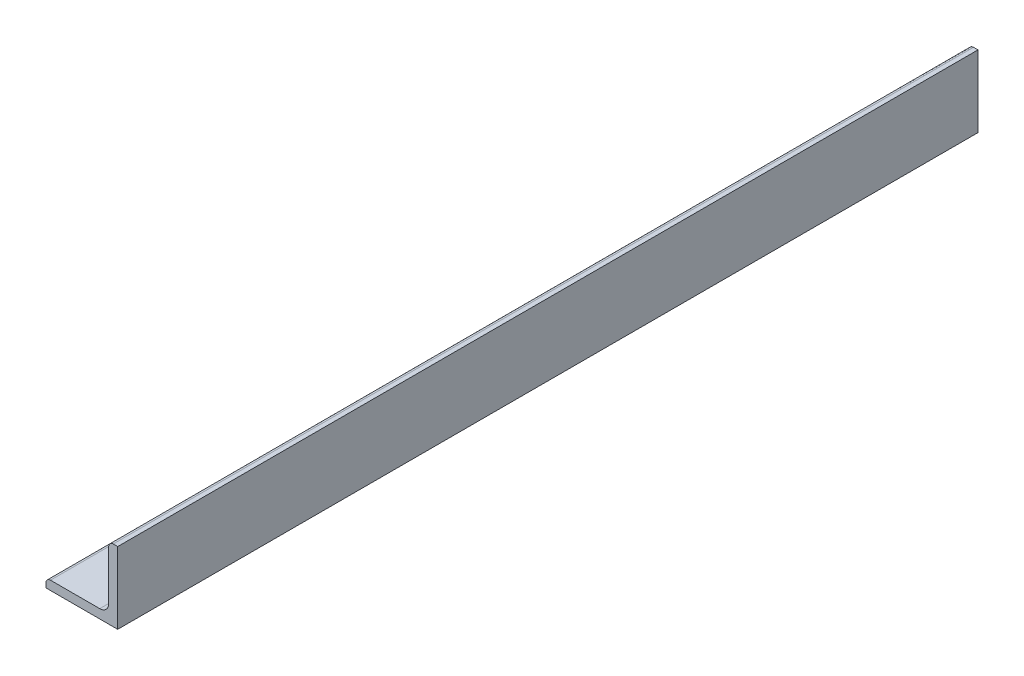
SolidWorks part; units mm, degrees
ref_plane "Front Plane" through (0, 0, 0) normal (0, 0, 1) x (1, 0, 0)
ref_plane "Top Plane" through (0, 0, 0) normal (0, 1, 0) x (1, 0, 0)
ref_plane "Right Plane" through (0, 0, 0) normal (1, 0, 0) x (0, 0, -1)
sketch "Sketch0" plane through (0, 0, 0) normal (0, 0, 1) x (1, 0, 0)
  line L0 (-12.7, -12.7) -> (12.7, -12.7)
  line L1 (12.7, -12.7) -> (12.7, 12.7)
  line L2 (12.7, 0) -> (0, 0) construction
  line L3 (0, 0) -> (0, -12.7) construction
  line L4 (9.525, -6.35) -> (9.525, 12.7) construction
  line L5 (6.35, -9.525) -> (-12.7, -9.525) construction
  arc A0 (9.525, -6.35) -> (6.35, -9.525) centre (6.35, -6.35) cw
  point P3 (8.5951, -8.5951)
  dimension "Inside Corner Radius" = 3.175
  dimension "Outside Height" = 25.4
  dimension "Inside Height" = 22.225
  dimension "Inside Width" = 22.225
  dimension "Wall Thickness" = 3.175
  dimension "D1" = 3.175
  dimension "Outside Width" = 25.4
sketch "Sketch1" plane through (0, 0, 0) normal (1, 0, 0) x (0, 0, -1)
  line L0 (152.4, 0) -> (-152.4, 0)
  point P4 (0, 0)
  dimension "Length" = 304.8
sketch "Sketch2" plane through (0, 0, 0) normal (0, 0, 1) x (1, 0, 0)
  line L0 (-12.7, -12.7) -> (12.7, -12.7)
  line L1 (12.7, -12.7) -> (12.7, 12.7)
  line L2 (12.7, 12.7) -> (9.525, 12.7) construction
  line L3 (9.525, 11.1125) -> (9.525, -6.35)
  line L4 (6.35, -9.525) -> (-11.1125, -9.525)
  line L5 (-12.7, -12.7) -> (-12.7, -9.525) construction
  line L6 (11.1125, 12.7) -> (12.7, 12.7)
  line L7 (-12.7, -11.1125) -> (-12.7, -12.7)
  line L8 (12.7, 0) -> (0, 0) construction
  line L9 (0, 0) -> (0, -12.7) construction
  arc A0 (9.525, 11.1125) -> (11.1125, 12.7) centre (11.1125, 11.1125) cw
  arc A1 (-12.7, -11.1125) -> (-11.1125, -9.525) centre (-11.1125, -11.1125) cw
  arc A2 (9.525, -6.35) -> (6.35, -9.525) centre (6.35, -6.35) cw
  dimension "Inside Radius" = 3.175
  dimension "Height" = 25.4
  dimension "Width" = 25.4
  dimension "Thickness" = 3.175
extrude "Boss-Extrude1" add sketch "Sketch2" along normal mid plane 304.8
sketch "Break Locations" plane through (0, 0, 0) normal (1, 0, 0) x (0, 0, -1)
  line L0 (-126.492, 0) -> (126.492, 0)
  line L1 (-152.4, -12.7) -> (-152.4, 12.7) construction
  line L2 (152.4, -12.7) -> (152.4, 12.7) construction
  point P0 (-130.81, 0)
  point P1 (130.81, 0)
  point P10 (0, 0)
  point P11 (126.492, 0)
  point P13 (-126.492, 0)
  dimension "D1" = 21.59
  dimension "D2" = 21.59
  dimension "D3" = 25.908
equation "\"D1@Break Locations\" = .85 * \"Height@Sketch2\""
equation "\"D2@Break Locations\"=\"D1@Break Locations\""
equation "\"Thickness@Sketch2\"=\"wall thickness@sketch0\""
equation "\"Height@Sketch2\"=\"outside height@sketch0\""
equation "\"Width@Sketch2\"=\"outside width@sketch0\""
equation "\"Inside Radius@Sketch2\"=\"inside corner radius@sketch0\""
equation "\"Length@Boss-Extrude1\"=\"length@sketch1\""
equation "\"D3@Break Locations\"=\"D2@Break Locations\"*1.2"
equation "\"D1@Sketch0\"=\"Wall Thickness@Sketch0\""
